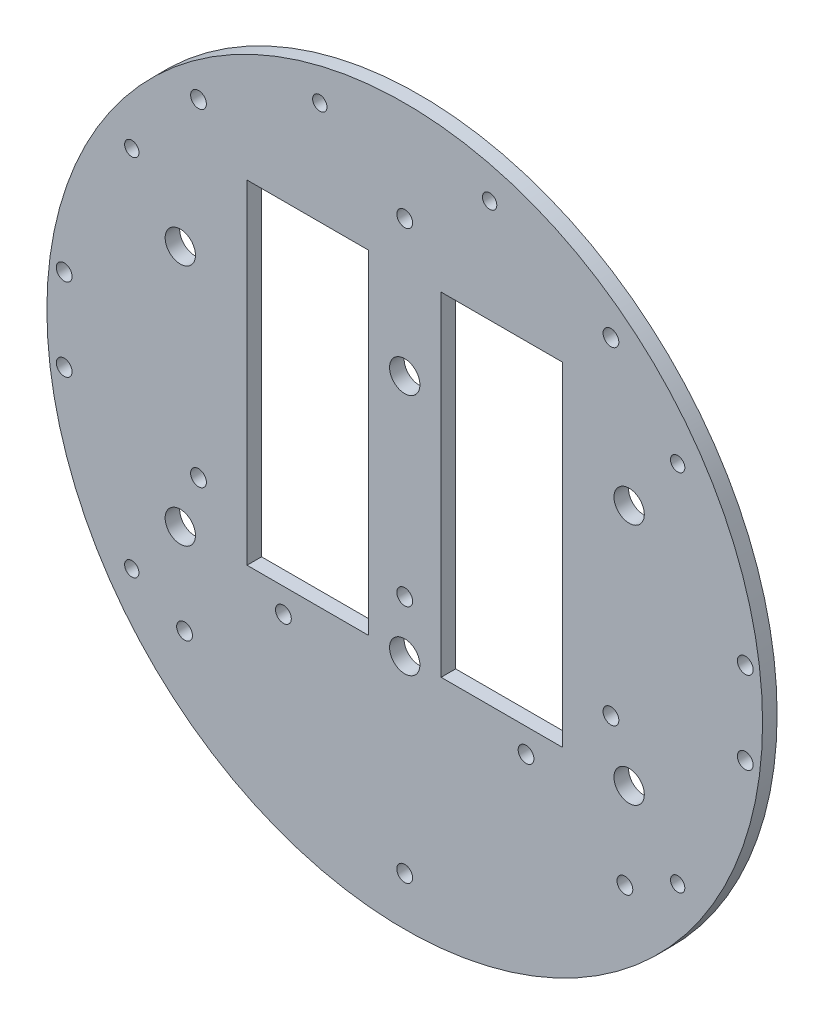
SolidWorks part; units mm, degrees
ref_plane "Front Plane" through (0, 0, 0) normal (0, 0, 1) x (1, 0, 0)
ref_plane "Top Plane" through (0, 0, 0) normal (0, 1, 0) x (1, 0, 0)
ref_plane "Right Plane" through (0, 0, 0) normal (1, 0, 0) x (0, 0, -1)
sketch "Sketch1" plane through (0, 0, 0) normal (0, 0, 1) x (1, 0, 0)
  line L0 (0, 0) -> (-82.1241, 0) construction
  line L1 (0, 0) -> (0, 95.6219) construction
  line L3 (-73.8459, 12.7) -> (-56.0659, 12.7)
  line L5 (-73.8459, -12.7) -> (-56.0659, -12.7)
  line L6 (-56.0659, 12.7) -> (-56.0659, -12.7)
  line L7 (73.8459, -12.7) -> (56.0659, -12.7)
  line L8 (73.8459, 12.7) -> (56.0659, 12.7)
  line L9 (56.0659, 12.7) -> (56.0659, -12.7)
  arc A0 (-73.8459, -12.7) -> (73.8459, -12.7) centre (0, 0) ccw
  circle A1 centre (-45.466, 11.049) radius 1.651
  circle A2 centre (-20.0673, 10.795) radius 1.651
  circle A3 centre (-20.0673, -10.795) radius 1.651
  circle A4 centre (-45.466, -11.049) radius 1.651
  circle A5 centre (45.466, -11.049) radius 1.651
  circle A6 centre (20.0673, -10.795) radius 1.651
  circle A7 centre (20.0673, 10.795) radius 1.651
  circle A8 centre (45.466, 11.049) radius 1.651
  arc A9 (73.8459, 12.7) -> (-73.8459, 12.7) centre (0, 0) ccw
  dimension "D2" = 3.302
  dimension "D3" = 3.302
  dimension "D4" = 25.4
  dimension "D5" = 10.795
  dimension "D10" = 45.466
  dimension "D6" = 25.4
  dimension "D7" = 17.78
  dimension "D8" = 74.93
  dimension "D9" = 74.93
  dimension "D11" = 12.7
extrude "Boss-Extrude2" add sketch "Sketch1" along normal blind 3.048
sketch "Sketch3" plane through (0, 0, 0) normal (0, 0, -1) x (-1, 0, 0)
  line L0 (0, 0) -> (0, -116.2908) construction
  line L1 (0, 0) -> (-153.8039, 0) construction
  line L2 (0, 0) -> (15.2681, -56.9814) construction
  line L3 (0, 0) -> (15.2302, -26.3795) construction
  circle A1 centre (0, -13.208) radius 12.1285
  circle A2 centre (0, 13.208) radius 12.1285
  circle A4 centre (-43.1052, -43.1052) radius 12.1285
  circle A6 centre (19.05, -32.9956) radius 12.1285
  circle A7 centre (19.05, 32.9956) radius 12.1285
  circle A8 centre (-43.1052, 43.1052) radius 12.1285
  circle A11 centre (43.1052, 43.1052) radius 12.1285
  circle A12 centre (-19.05, 32.9956) radius 12.1285
  circle A13 centre (-19.05, -32.9956) radius 12.1285
  circle A14 centre (43.1052, -43.1052) radius 12.1285
  point P36 (0, 0)
  point P53 (0, 0)
  point P55 (0, 0)
  dimension "D1" = 24.257
  dimension "D2" = 24.257
  dimension "D4" = 15
  dimension "D6" = 0
  dimension "D8" = 24.257
  dimension "D9" = 30
  dimension "D10" = 13.208
  dimension "D11" = 13.208
extrude "Cut-Extrude2" [suppressed] cut sketch "Sketch3" against normal through all
sketch "Sketch5" plane through (0, 0, 0) normal (0, 0, -1) x (-1, 0, 0)
  line L1 (16.7319, 15.0155) -> (52.8378, 15.0155)
  line L2 (16.7319, 15.0155) -> (16.7319, -15.7858)
  line L3 (16.7319, -15.7858) -> (52.8378, -15.7858)
  line L4 (52.8378, 15.0155) -> (52.8378, -15.7858)
  line L5 (-50.8098, 17.6836) -> (-14.8513, 17.6836)
  line L6 (-50.8098, 17.6836) -> (-50.8098, -15.7858)
  line L7 (-50.8098, -15.7858) -> (-14.8513, -15.7858)
  line L8 (-14.8513, 17.6836) -> (-14.8513, -15.7858)
extrude "Boss-Extrude4" add sketch "Sketch5" against normal up to surface (3.048 mm away) up to face at (18.4163, 10.795, 3.048)
extrude "Cut-Extrude6" cut sketch "Sketch10" against normal blind 16.51
sketch "Sketch10" plane through (31.3134, -132.614, 6.35) normal (0, 0, 1) x (0, -1, 0)
  line L0 (-122.6703, -31.3134) -> (-122.6703, -98.8476) construction
  line L1 (-122.6703, -31.3134) -> (-20.2053, -31.3134) construction
  circle A1 centre (-188.7103, -31.3134) radius 1.651
  circle A2 centre (-56.6303, -31.3134) radius 1.651
  circle A3 centre (-122.6703, -82.1134) radius 1.651
  circle A4 centre (-122.6703, 19.4866) radius 1.651
sketch "Sketch11" plane through (0, 0, 0) normal (0, 0, -1) x (-1, 0, 0)
  line L0 (0, 108.17) -> (0, -126.4139) construction
  line L1 (-105.217, 0) -> (120.8442, 0) construction
  circle A0 centre (43.18, 53.975) radius 1.651
  circle A1 centre (0, 53.975) radius 1.651
  circle A2 centre (0, -14.605) radius 1.651
  circle A3 centre (43.18, -14.605) radius 1.651
  circle A4 centre (-43.18, 53.975) radius 1.651
  circle A5 centre (-43.18, -14.605) radius 1.651
  circle A6 centre (-25.4, -30.48) radius 1.651
  circle A7 centre (-46.101, -43.861) radius 1.651
  circle A8 centre (46.101, -43.861) radius 1.651
  circle A9 centre (0, -64.77) radius 1.651
  circle A10 centre (25.4, -30.48) radius 1.651
  dimension "D1" = 3.302
  dimension "D2" = 3.302
  dimension "D6" = 43.18
  dimension "D3" = 3.302
  dimension "D4" = 3.302
  dimension "D5" = 3.302
  dimension "D8" = 3.302
  dimension "D10" = 53.975
  dimension "D11" = 34.29
  dimension "D12" = 3.302
  dimension "D13" = 3.302
  dimension "D14" = 3.302
  dimension "D20" = 3.302
  dimension "D7" = 68.58
  dimension "D9" = 43.18
  dimension "D15" = 92.202
  dimension "D16" = 46.101
  dimension "D17" = 25.4
  dimension "D18" = 30.48
  dimension "D21" = 68.58
  dimension "D22" = 43.18
extrude "Cut-Extrude7" cut sketch "Sketch11" against normal through all
sketch "Sketch12" plane through (0, 0, 0) normal (0, 0, -1) x (-1, 0, 0)
  line L0 (-54.9953, 50.8923) -> (-54.5665, -51.3518)
  line L1 (54.9953, 50.8923) -> (54.9953, -50.8923)
  arc A0 (-54.9953, 50.8923) -> (-54.5665, -51.3518) centre (0, 0) ccw
  circle A1 centre (0, 0) radius 74.93 construction
  arc A2 (54.9953, -50.8923) -> (54.9953, 50.8923) centre (0, 0) ccw
extrude "Boss-Extrude6" add sketch "Sketch12" against normal up to surface (3.048 mm away) up to face at (23.749, -30.48, 3.048)
sketch "Sketch14" plane through (0, 0, 0) normal (0, 0, -1) x (-1, 0, 0)
  line L0 (0, 0) -> (0, 87.4947) construction
  line L1 (-33.02, 44.45) -> (-7.62, 44.45)
  line L2 (-33.02, 44.45) -> (-33.02, -25.4)
  line L3 (-33.02, -25.4) -> (-7.62, -25.4)
  line L4 (-7.62, 44.45) -> (-7.62, -25.4)
  line L5 (33.02, -25.4) -> (7.62, -25.4)
  line L6 (7.62, 44.45) -> (7.62, -25.4)
  line L7 (33.02, 44.45) -> (33.02, -25.4)
  line L8 (33.02, 44.45) -> (7.62, 44.45)
  dimension "D1" = 25.4
  dimension "D2" = 69.85
  dimension "D3" = 44.45
  dimension "D4" = 33.02
extrude "Cut-Extrude9" cut sketch "Sketch14" against normal blind 46.482
extrude "Cut-Extrude10" cut sketch "Sketch15" against normal blind 150.876
sketch "Sketch15" plane through (-30.092, 4.0835, -68.453) normal (0, 0, -1) x (-1, 0, 0)
  circle A0 centre (-101.396, -12.7195) radius 1.651
  circle A1 centre (-101.396, 4.5525) radius 1.651
  circle A2 centre (41.212, -12.7195) radius 1.651
  circle A3 centre (41.212, 4.5525) radius 1.651
sketch "Sketch16" plane through (0, 0, 0) normal (0, 0, -1) x (-1, 0, 0)
  line L0 (0, 93.6412) -> (0, -85.2267) construction
  line L1 (-93.0402, 0) -> (98.0888, 0) construction
  circle A0 centre (-17.78, 66.04) radius 1.5
  circle A1 centre (-57.15, 38.1) radius 1.5
  circle A2 centre (17.78, 66.04) radius 1.5
  circle A3 centre (-57.15, -38.1) radius 1.5
  circle A4 centre (57.15, -38.1) radius 1.5
  circle A5 centre (57.15, 38.1) radius 1.5
  dimension "D1" = 3
  dimension "D2" = 3
  dimension "D3" = 17.78
  dimension "D4" = 66.04
  dimension "D5" = 38.1
  dimension "D6" = 57.15
extrude "Cut-Extrude11" cut sketch "Sketch16" against normal through all
extrude "Cut-Extrude12" cut sketch "Sketch17" against normal blind 48.768 and the other way blind 103.378
sketch "Sketch17" plane through (-30.092, 4.0835, -57.658) normal (0, 0, 1) x (1, 0, 0)
  line L0 (30.092, -4.0835) -> (148.6336, -4.0835) construction
  line L1 (30.092, -4.0835) -> (30.092, 90.452) construction
  circle A0 centre (-16.898, 21.3165) radius 3.175
  circle A1 centre (77.082, 21.3165) radius 3.175
  circle A2 centre (30.092, 21.3165) radius 3.175
  circle A4 centre (77.082, -29.4835) radius 3.175
  circle A5 centre (30.092, -29.4835) radius 3.175
  circle A6 centre (-16.898, -29.4835) radius 3.175
